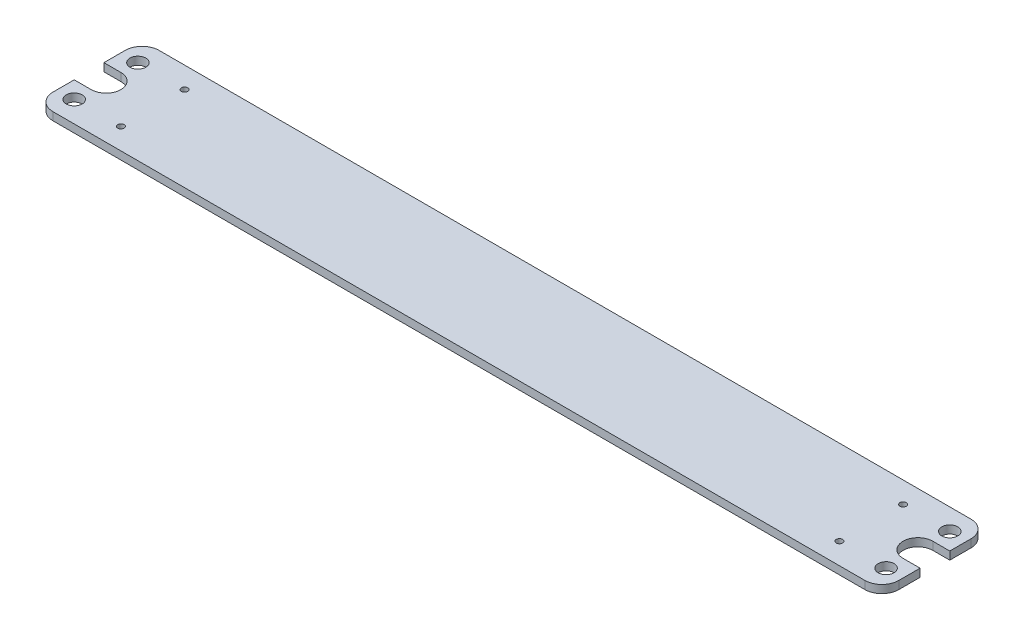
SolidWorks part; units mm, degrees
ref_plane "Front Plane" through (0, 0, 0) normal (0, 0, 1) x (1, 0, 0)
ref_plane "Top Plane" through (0, 0, 0) normal (0, 1, 0) x (1, 0, 0)
ref_plane "Right Plane" through (0, 0, 0) normal (1, 0, 0) x (0, 0, -1)
sketch "Sketch1" plane through (0, 0, 0) normal (0, 1, 0) x (1, 0, 0)
  line L0 (0, -31.75) -> (1.27, -31.75) construction
  line L1 (10.16, 0) -> (253.0475, 0)
  line L2 (0, -10.16) -> (0, -22.86)
  line L3 (10.16, -63.5) -> (253.0475, -63.5)
  line L5 (10.16, -40.64) -> (0, -40.64)
  line L6 (10.16, -22.86) -> (0, -22.86)
  line L7 (0, -40.64) -> (0, -53.34)
  line L8 (19.05, -31.75) -> (87.4324, -31.75) construction
  line L14 (253.0475, -63.5) -> (253.0475, 0)
  circle A0 centre (10.16, -50.8) radius 4.7625
  circle A1 centre (10.16, -12.7) radius 4.7625
  arc A2 (10.16, -40.64) -> (10.16, -22.86) centre (10.16, -31.75) ccw
  circle A3 centre (10.16, -12.7) radius 6.35 construction
  circle A4 centre (10.16, -50.8) radius 6.35 construction
  arc A5 (0, -53.34) -> (10.16, -63.5) centre (10.16, -53.34) ccw
  arc A6 (10.16, 0) -> (0, -10.16) centre (10.16, -10.16) ccw
  circle A7 centre (38.1, -50.8) radius 1.905
  circle A8 centre (38.1, -12.7) radius 1.905
  point P1 (0, -16.51)
  point P22 (0, -63.5)
  point P25 (0, 0)
  point P38 (50.8, -63.5)
  dimension "D3" = 9.525
  dimension "D4" = 9.525
  dimension "D5" = 17.78
  dimension "D10" = 31.75
  dimension "D11" = 12.7
  dimension "D12" = 12.7
  dimension "D13" = 10.16
  dimension "D14" = 3.81
  dimension "D15" = 3.81
  dimension "D1" = 63.5
  dimension "D2" = 50.8
  dimension "D6" = 19.05
  dimension "D7" = 19.05
  dimension "D8" = 10.16
  dimension "D9" = 10.16
  dimension "D16" = 12.7
  dimension "D17" = 12.7
  dimension "D18" = 253.0475
  dimension "D19" = 253.0475
  dimension "D20" = 38.1
extrude "Boss-Extrude1" add sketch "Sketch1" along normal blind 4.7625
mirror "Mirror1" about plane through (253.0475, 4.7625, 63.5) normal (-1, 0, 0) of "Boss-Extrude1"
